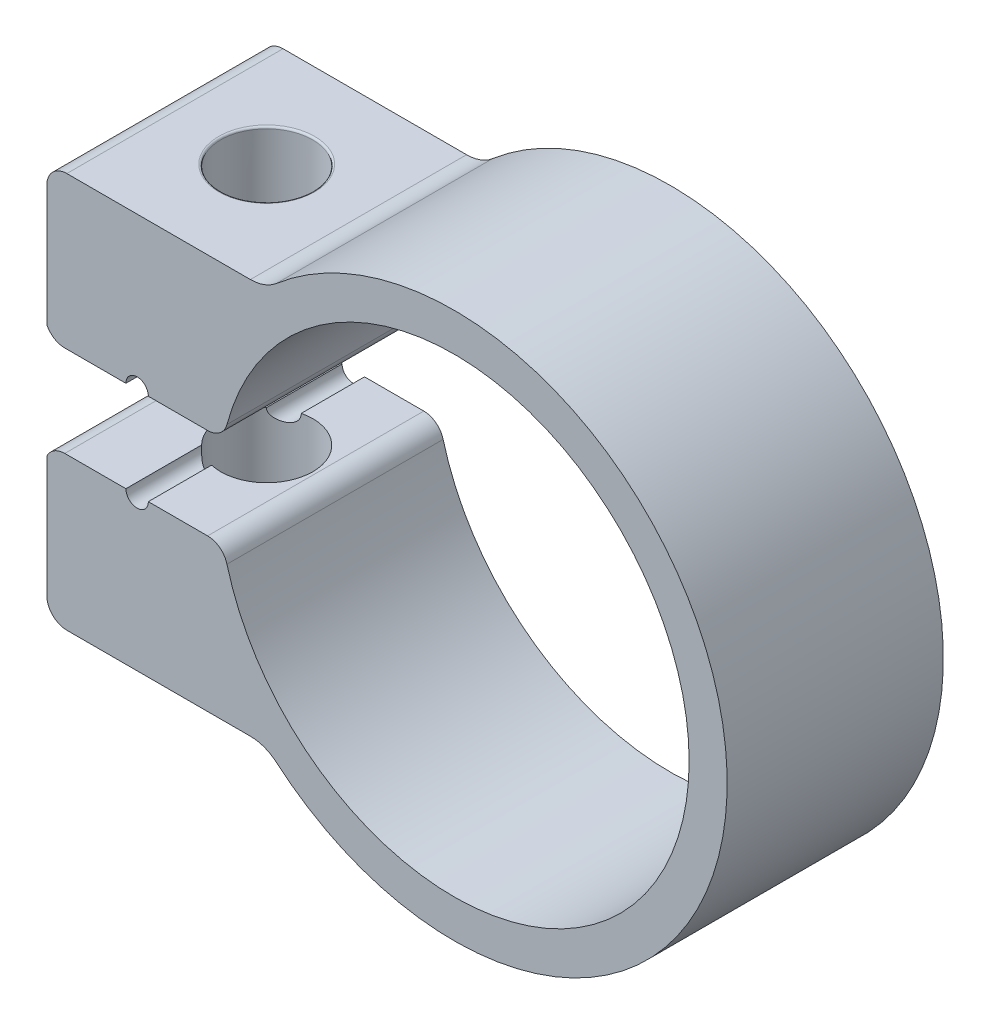
SolidWorks part; units mm, degrees
material "1060 Alloy"
ref_plane "Front Plane" through (0, 0, 0) normal (0, 0, 1) x (1, 0, 0)
ref_plane "Top Plane" through (0, 0, 0) normal (0, 1, 0) x (1, 0, 0)
ref_plane "Right Plane" through (0, 0, 0) normal (1, 0, 0) x (0, 0, -1)
sketch "Sketch1" plane through (0, 0, 0) normal (0, 0, 1) x (1, 0, 0)
  line L2 (-18.2867, -2.8956) -> (-14.4098, -2.8956)
  line L10 (-35.2737, 0) -> (57.228, 0) construction
  line L11 (-19.4268, -3.6063) -> (-19.4268, -11.2776)
  line L12 (-18.1568, -12.5476) -> (-6.5103, -12.5476)
  line L13 (-12.9861, -2.8956) -> (-9.2241, -2.8956)
  line L14 (-12.9861, 2.8956) -> (-9.2241, 2.8956)
  line L15 (-19.4268, 3.6063) -> (-19.4268, 11.2776)
  line L16 (-18.2867, 2.8956) -> (-14.4098, 2.8956)
  line L17 (-18.1568, 12.5476) -> (-6.5103, 12.5476)
  arc A0 (-4.8578, -13.1586) -> (23.6899, 1.3208) centre (6.414, 0) ccw
  arc A2 (-7.9968, -3.8387) -> (21.2687, 1.3208) centre (6.414, 0) ccw
  arc A3 (-19.4268, -3.6063) -> (-18.2867, -2.8956) centre (-18.2867, -4.1656) cw
  arc A4 (-9.2241, -2.8956) -> (-7.9968, -3.8387) centre (-9.2241, -4.1656) cw
  arc A5 (-14.4098, -2.8956) -> (-12.9861, -2.8956) centre (-13.6979, -2.8956) ccw
  arc A6 (-6.5103, -12.5476) -> (-4.8578, -13.1586) centre (-6.5103, -15.0876) cw
  arc A7 (-18.1568, -12.5476) -> (-19.4268, -11.2776) centre (-18.1568, -11.2776) cw
  arc A8 (-14.4098, 2.8956) -> (-12.9861, 2.8956) centre (-13.6979, 2.8956) cw
  arc A9 (-9.2241, 2.8956) -> (-7.9968, 3.8387) centre (-9.2241, 4.1656) ccw
  arc A10 (-19.4268, 3.6063) -> (-18.2867, 2.8956) centre (-18.2867, 4.1656) ccw
  arc A11 (-7.9968, 3.8387) -> (21.2687, 1.3208) centre (6.414, 0) cw
  arc A12 (-4.8578, 13.1586) -> (23.6899, 1.3208) centre (6.414, 0) cw
  arc A13 (-18.1568, 12.5476) -> (-19.4268, 11.2776) centre (-18.1568, 11.2776) ccw
  arc A14 (-6.5103, 12.5476) -> (-4.8578, 13.1586) centre (-6.5103, 15.0876) ccw
  point P5 (-13.2586, -12.5476)
  point P35 (-13.2586, 12.5476)
  dimension "D2" = 2.413
  dimension "D4" = 2.54
  dimension "D5" = 1.27
  dimension "D6" = 1.27
  dimension "D1" = 9.652
  dimension "D3" = 11.43
  dimension "D7" = 5.7912
extrude "Boss-Extrude1" add sketch "Sketch1" along normal blind 13.716
sketch "Sketch2" plane through (0, -12.5476, 0) normal (0, -1, 0) x (1, 0, 0)
  line L0 (-18.1568, 0) -> (-6.5103, 0) construction
  line L1 (-6.5103, 13.716) -> (-6.5103, 0) construction
  circle A0 centre (-12.3336, 6.858) radius 5.4864
  point P4 (-12.3336, 0)
  point P8 (-6.5103, 6.858)
  dimension "D1" = 10.9728
extrude "Cut-Extrude1" cut sketch "Sketch2" against normal blind 3.6068
sketch "Sketch3" plane through (0, -8.9408, 0) normal (0, -1, 0) x (1, 0, 0)
  circle A0 centre (-12.3336, 6.858) radius 2.921
  dimension "D1" = 5.842
extrude "Cut-Extrude2" cut sketch "Sketch3" against normal through all
fillet "Fillet1" radius 0.127 1 edges at (-9.4126, 12.5476, 6.858)
fillet "Fillet2" radius 0.127 1 edges at (-6.8472, -12.5476, 6.858)
fillet "Fillet3" radius 1.27 1 edges at (-6.8472, -8.9408, 6.858)
fillet "Fillet4" radius 0.127 1 edges at (-9.4126, -8.9408, 6.858)
